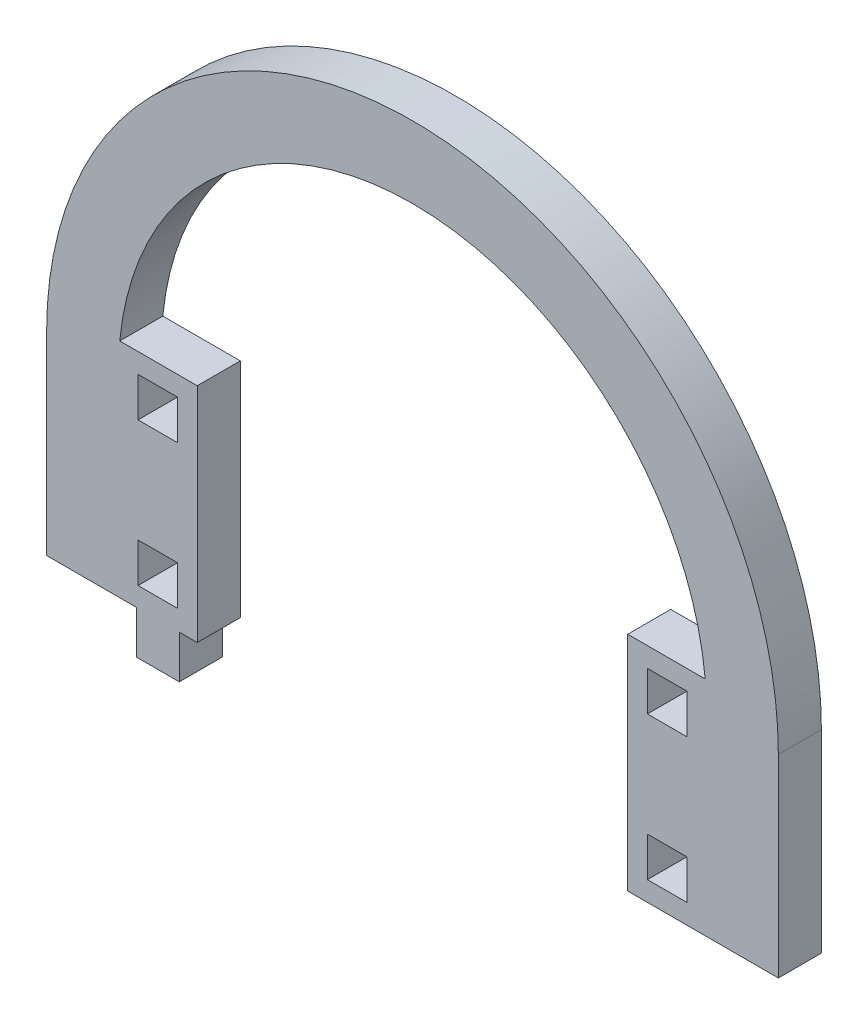
SolidWorks part; units mm, degrees
ref_plane "Front Plane" through (0, 0, 0) normal (0, 0, 1) x (1, 0, 0)
ref_plane "Top Plane" through (0, 0, 0) normal (0, 1, 0) x (1, 0, 0)
ref_plane "Right Plane" through (0, 0, 0) normal (1, 0, 0) x (0, 0, -1)
sketch "Model" plane through (0, 0, 0) normal (0, 0, 1) x (1, 0, 0)
  line L0 (3179.4987, 1276.7818) -> (3179.4987, 1249.7818)
  line L1 (3281.4987, 1276.7818) -> (3281.4987, 1249.7818)
  line L2 (3271.4987, 1249.7818) -> (3281.4987, 1249.7818)
  line L3 (3268.7487, 1258.0318) -> (3263.2487, 1258.0318)
  line L4 (3263.2487, 1258.0318) -> (3263.2487, 1252.5318)
  line L5 (3263.2487, 1252.5318) -> (3268.7487, 1252.5318)
  line L6 (3268.7487, 1252.5318) -> (3268.7487, 1258.0318)
  line L7 (3260.4987, 1249.7818) -> (3271.4987, 1249.7818)
  line L8 (3268.7487, 1278.0318) -> (3263.2487, 1278.0318)
  line L9 (3263.2487, 1278.0318) -> (3263.2487, 1272.5318)
  line L10 (3263.2487, 1272.5318) -> (3268.7487, 1272.5318)
  line L11 (3268.7487, 1272.5318) -> (3268.7487, 1278.0318)
  line L12 (3271.3031, 1280.7818) -> (3260.4987, 1280.7818)
  line L13 (3197.7487, 1258.0318) -> (3192.2487, 1258.0318)
  line L14 (3192.2487, 1258.0318) -> (3192.2487, 1252.5318)
  line L15 (3192.2487, 1252.5318) -> (3197.7487, 1252.5318)
  line L16 (3197.7487, 1252.5318) -> (3197.7487, 1258.0318)
  line L17 (3197.9987, 1249.7818) -> (3200.4987, 1249.7818)
  line L18 (3191.9987, 1249.7818) -> (3191.9987, 1243.7818)
  line L19 (3191.9987, 1243.7818) -> (3197.9987, 1243.7818)
  line L20 (3197.9987, 1243.7818) -> (3197.9987, 1249.7818)
  line L21 (3197.7487, 1278.0318) -> (3192.2487, 1278.0318)
  line L22 (3192.2487, 1278.0318) -> (3192.2487, 1272.5318)
  line L23 (3192.2487, 1272.5318) -> (3197.7487, 1272.5318)
  line L24 (3197.7487, 1272.5318) -> (3197.7487, 1278.0318)
  line L25 (3200.4987, 1280.7818) -> (3189.6943, 1280.7818)
  line L26 (3200.4987, 1280.7818) -> (3200.4987, 1249.7818)
  line L27 (3260.4987, 1280.7818) -> (3260.4987, 1249.7818)
  line L28 (3179.4987, 1249.7818) -> (3191.9987, 1249.7818)
  arc A0 (3281.4987, 1276.7818) -> (3179.4987, 1276.7818) centre (3230.4987, 1276.7818) ccw
  arc A1 (3271.3031, 1280.7818) -> (3189.6943, 1280.7818) centre (3230.4987, 1276.7818) ccw
extrude "Boss-Extrude1" add sketch "Model" along normal blind 6 contours L23 L24 L21 L22 | L15 L16 L13 L14 | L10 L11 L8 L9 | L5 L6 L3 L4 | L0 L28 L18 L19 L20 L17 L26 L25 A1 L12 L27 L7 L2 L1 A0
